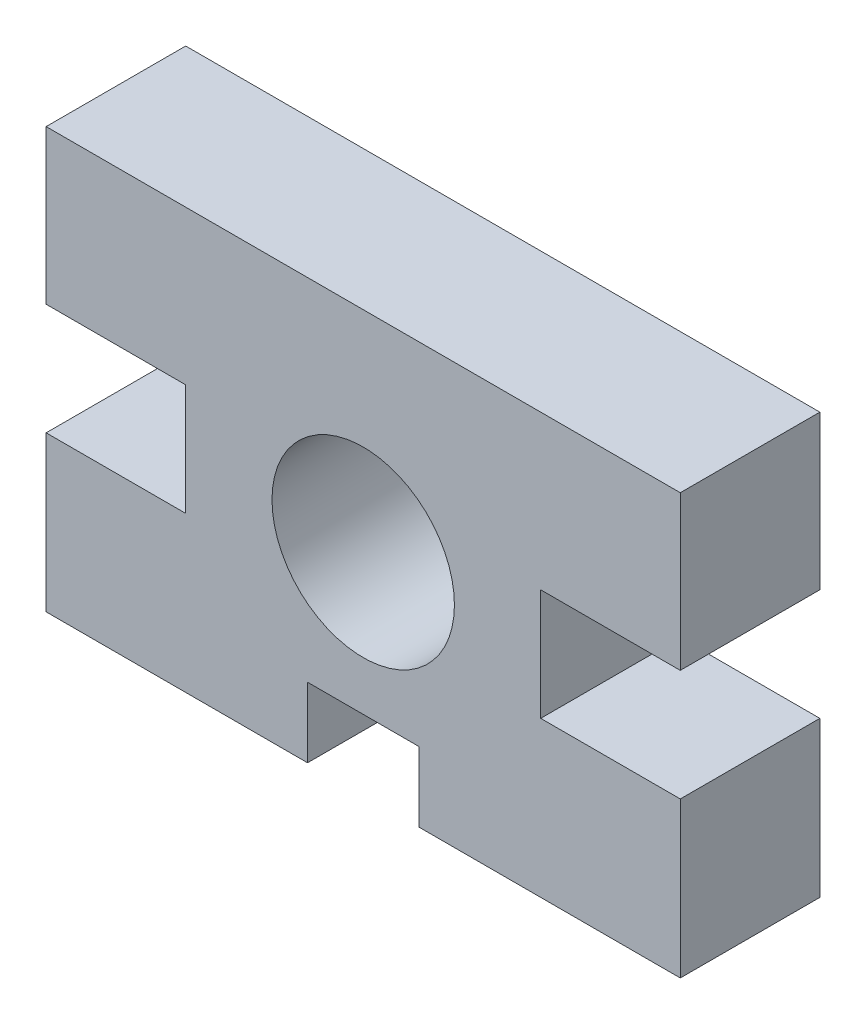
SolidWorks part; units mm, degrees
ref_plane "Front Plane" through (0, 0, 0) normal (0, 0, 1) x (1, 0, 0)
ref_plane "Top Plane" through (0, 0, 0) normal (0, 1, 0) x (1, 0, 0)
ref_plane "Right Plane" through (0, 0, 0) normal (1, 0, 0) x (0, 0, -1)
sketch "Sketch1" plane through (0, 0, 0) normal (0, 0, 1) x (1, 0, 0)
  line L0 (-14.425, 9.56) -> (-14.425, 2.56)
  line L1 (-14.425, 9.56) -> (14.425, 9.56)
  line L2 (-14.425, 9.56) -> (-14.425, -9.56) construction
  line L3 (-14.425, -9.56) -> (14.425, -9.56) construction
  line L5 (-14.425, -9.56) -> (-14.425, -2.5051)
  line L6 (-14.425, -2.5051) -> (-8.075, -2.5051)
  line L7 (-8.075, -2.5051) -> (-8.075, 2.56)
  line L8 (-8.075, 2.56) -> (-14.425, 2.56)
  line L9 (0, 0) -> (0, 9.56) construction
  line L10 (14.425, -9.56) -> (14.425, -2.5051)
  line L11 (8.075, -2.5051) -> (8.075, 2.56)
  line L12 (8.075, 2.56) -> (14.425, 2.56)
  line L13 (14.425, 9.56) -> (14.425, 2.56)
  line L14 (14.425, -2.5051) -> (8.075, -2.5051)
  line L15 (-2.5325, -9.56) -> (-2.5325, -6.385)
  line L16 (0, -6.385) -> (-2.5325, -6.385)
  line L17 (2.5325, -6.385) -> (2.5325, -9.56)
  line L18 (0, 0) -> (0, -9.56) construction
  line L19 (0, -6.385) -> (2.5325, -6.385)
  line L20 (2.5325, -9.56) -> (14.425, -9.56)
  line L21 (-14.425, -9.56) -> (-2.5325, -9.56)
  circle A0 centre (0, 0) radius 4.15
  point P0 (0, 0)
  dimension "D3" = 8.3
  dimension "D1" = 11.8925
  dimension "D2" = 19.12
  dimension "D4" = 7
  dimension "D5" = 6.35
  dimension "D6" = 5.0651
  dimension "D7" = 3.175
  dimension "D8" = 5.065
  dimension "D9" = 2.5325
extrude "Boss-Extrude1" add sketch "Sketch1" along normal blind 6.35
